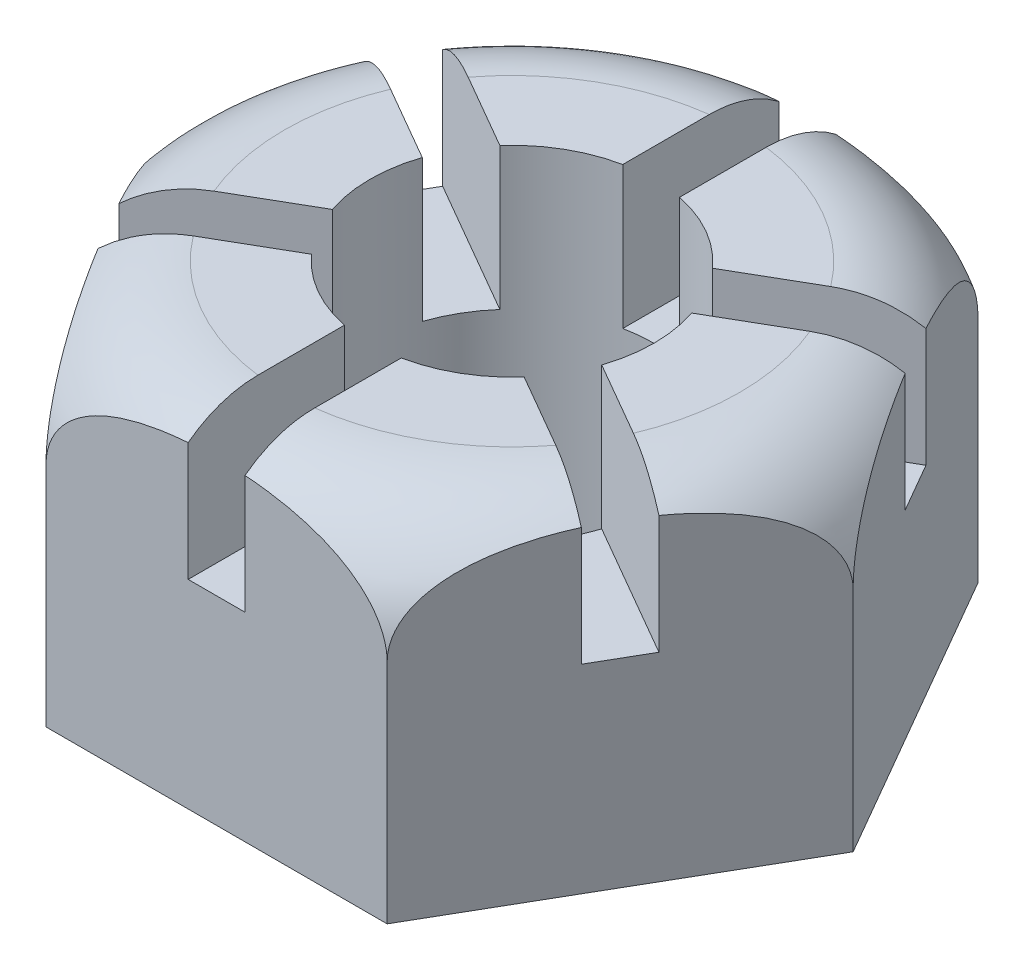
SolidWorks part; units mm, degrees
ref_plane "Front Plane" through (0, 0, 0) normal (0, 0, 1) x (1, 0, 0)
ref_plane "Top Plane" through (0, 0, 0) normal (0, 1, 0) x (1, 0, 0)
ref_plane "Right Plane" through (0, 0, 0) normal (1, 0, 0) x (0, 0, -1)
sketch "Sketch1" plane through (0, 0, 0) normal (0, 1, 0) x (1, 0, 0)
  line L1 (60.0444, 0) -> (30.0222, 52)
  line L2 (30.0222, 52) -> (-30.0222, 52)
  line L3 (-30.0222, 52) -> (-60.0444, 0)
  line L4 (-60.0444, 0) -> (-30.0222, -52)
  line L5 (-30.0222, -52) -> (30.0222, -52)
  line L6 (30.0222, -52) -> (60.0444, 0)
  circle A0 centre (0, 0) radius 52 construction
  circle A1 centre (0, 0) radius 25
  dimension "D2" = 50
  dimension "D1" = 104
extrude "Boss-Extrude1" add sketch "Sketch1" along normal mid plane 60
sketch "Sketch2" plane through (0, 0, 0) normal (0, 0, 1) x (1, 0, 0)
  line L0 (-40.0444, 30) -> (-34.2082, 30)
  line L1 (-60.0444, 30) -> (-30.0222, 30) construction
  line L2 (-34.2082, 30) -> (-58.8775, 44.8159)
  line L3 (-58.8775, 44.8159) -> (-76.3177, 24.773)
  line L4 (-76.3177, 24.773) -> (-60.0444, 5.345)
  line L5 (-60.0444, 30) -> (-60.0444, -30) construction
  line L6 (-60.0444, 5.345) -> (-60.0444, 10)
  line L7 (0, 0) -> (0, 46.339) construction
  arc A0 (-40.0444, 30) -> (-60.0444, 10) centre (-40.0444, 10) ccw
  point P12 (-60.0444, 30)
  dimension "D1" = 20
revolve "Cut-Revolve1" cut sketch "Sketch2" angle 360 about L7
sketch "Sketch5" plane through (0, 0, 0) normal (0, 0, 1) x (1, 0, 0)
  line L2 (-5, 30) -> (-5, 5)
  line L3 (5, 30) -> (5, 5)
  line L4 (-5, 30) -> (5, 30)
  line L5 (-5, 5) -> (5, 5)
extrude "Cut-Extrude1" cut sketch "Sketch5" against normal mid plane 135
pattern_circular "CirPattern1" count 6 over 360 about axis through (0, 0, 0) along (0, 1, 0) of "Cut-Extrude1"
